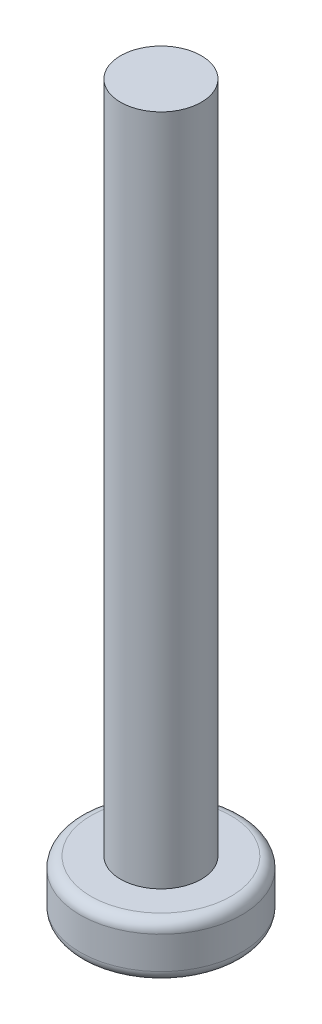
SolidWorks part; units mm, degrees
ref_plane "Front Plane" through (0, 0, 0) normal (0, 0, 1) x (1, 0, 0)
ref_plane "Top Plane" through (0, 0, 0) normal (0, 1, 0) x (1, 0, 0)
ref_plane "Right Plane" through (0, 0, 0) normal (1, 0, 0) x (0, 0, -1)
sketch "Sketch1" plane through (0, 0, 0) normal (0, 1, 0) x (1, 0, 0)
  circle A0 centre (0, 0) radius 3
  dimension "D1" = 6
extrude "Boss-Extrude1" add sketch "Sketch1" along normal blind 2
sketch "Sketch2" plane through (0, 2, 0) normal (0, 1, 0) x (1, 0, 0)
  circle A0 centre (0, 0) radius 1.5
  dimension "D1" = 3
extrude "Boss-Extrude2" add sketch "Sketch2" along normal blind 25
sketch "Sketch3" plane through (0, 0, 0) normal (0, -1, 0) x (-1, 0, 0)
  line L1 (0.45, -1.5) -> (-0.45, -1.5)
  line L2 (0.45, -1.5) -> (0.45, 1.5)
  line L3 (0.45, 1.5) -> (-0.45, 1.5)
  line L4 (-0.45, -1.5) -> (-0.45, 1.5)
  line L5 (1.5, -0.45) -> (-1.5, -0.45)
  line L6 (1.5, -0.45) -> (1.5, 0.45)
  line L7 (1.5, 0.45) -> (-1.5, 0.45)
  line L8 (-1.5, -0.45) -> (-1.5, 0.45)
  point P4 (0, -1.5)
  point P5 (0, 1.5)
  point P14 (1.5, 0)
  point P15 (-1.5, 0)
  dimension "D1" = 1.5
  dimension "D2" = 1.5
  dimension "D3" = 0.9
  dimension "D4" = 0.9
  dimension "D5" = 1.5
  dimension "D6" = 1.5
extrude "Cut-Extrude1" cut sketch "Sketch3" against normal blind 1.9 contours L2 L7 L4 L5 | L6 L7 L2 L5 | L2 L5 L4 L1 | L8 L5 L4 L7 | L7 L2 L3 L4
fillet "Fillet1" radius 0.4 2 edges at (0, 2, 3) (0, 0, 3)
